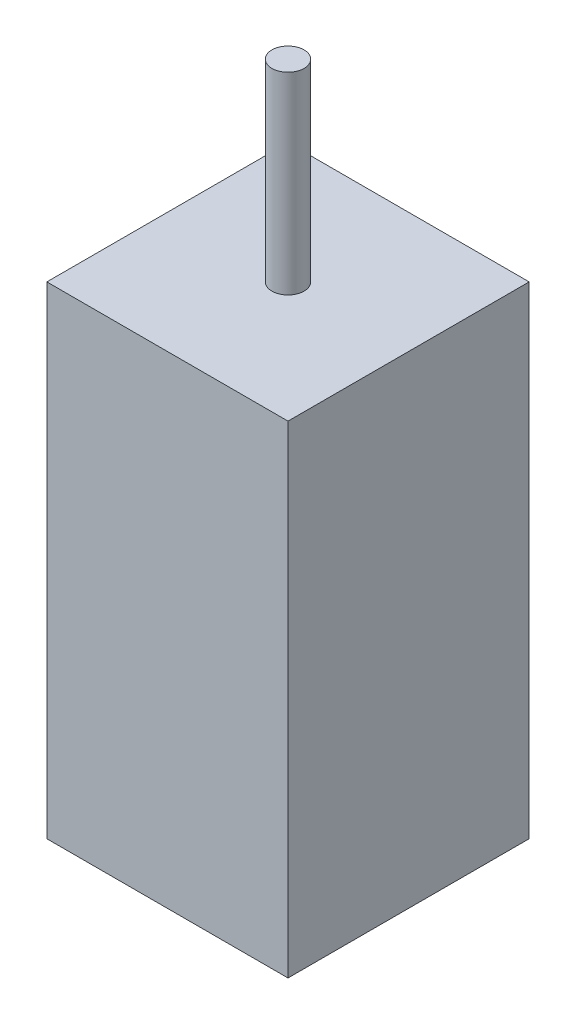
SolidWorks part; units mm, degrees
ref_plane "Front Plane" through (0, 0, 0) normal (0, 0, 1) x (1, 0, 0)
ref_plane "Top Plane" through (0, 0, 0) normal (0, 1, 0) x (1, 0, 0)
ref_plane "Right Plane" through (0, 0, 0) normal (1, 0, 0) x (0, 0, -1)
sketch "Sketch3" plane through (0, 0, 0) normal (0, 1, 0) x (1, 0, 0)
  line L1 (-7.5, 7.5) -> (7.5, 7.5)
  line L2 (-7.5, 7.5) -> (-7.5, -7.5)
  line L3 (-7.5, -7.5) -> (7.5, -7.5)
  line L4 (7.5, 7.5) -> (7.5, -7.5)
  line L5 (-7.5, 7.5) -> (7.5, -7.5) construction
  line L6 (-7.5, -7.5) -> (7.5, 7.5) construction
  point P0 (0, 0)
  dimension "D1" = 15
  dimension "D2" = 15
extrude "Boss-Extrude1" add sketch "Sketch3" along normal blind 30
sketch "Sketch4" plane through (0, 30, 0) normal (0, 1, 0) x (1, 0, 0)
  circle A0 centre (0, 0) radius 1
  dimension "D1" = 2
extrude "Boss-Extrude2" add sketch "Sketch4" along normal blind 12
